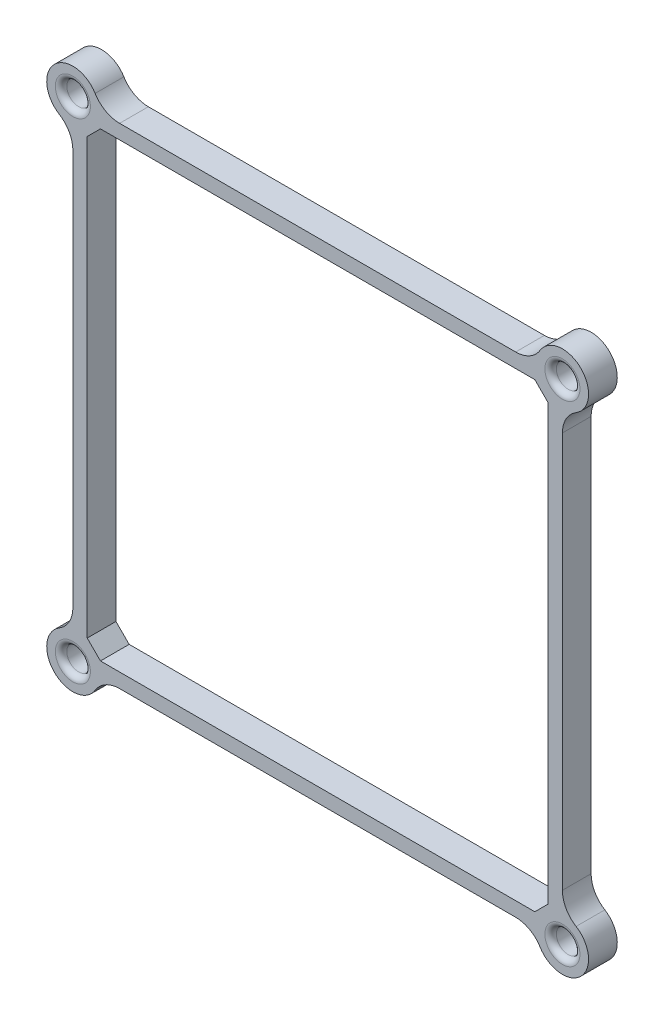
SolidWorks part; units mm, degrees
ref_plane "Front Plane" through (0, 0, 0) normal (0, 0, 1) x (1, 0, 0)
ref_plane "Top Plane" through (0, 0, 0) normal (0, 1, 0) x (1, 0, 0)
ref_plane "Right Plane" through (0, 0, 0) normal (1, 0, 0) x (0, 0, -1)
sketch "Sketch1" plane through (0, 0, 0) normal (0, 0, 1) x (1, 0, 0)
  line L0 (40.1, 0) -> (40.1, -80.2) construction
  line L1 (0, 0) -> (80.2, 0)
  line L2 (0, 0) -> (0, -80.2)
  line L3 (0, -80.2) -> (80.2, -80.2)
  line L4 (80.2, 0) -> (80.2, -80.2)
  line L6 (-2.5, 2.5) -> (82.7, 2.5)
  line L7 (-2.5, 2.5) -> (-2.5, -82.7)
  line L8 (-2.5, -82.7) -> (82.7, -82.7)
  line L9 (82.7, 2.5) -> (82.7, -82.7)
  line L10 (-2.5, 2.5) -> (82.7, -82.7) construction
  line L11 (-2.5, -82.7) -> (82.7, 2.5) construction
  circle A0 centre (-2.5, -82.7) radius 2.05
  circle A1 centre (-2.5, -82.7) radius 4.55
  circle A2 centre (82.7, -82.7) radius 2.05
  circle A3 centre (82.7, -82.7) radius 4.55
  circle A4 centre (82.7, 2.5) radius 2.05
  circle A5 centre (82.7, 2.5) radius 4.55
  circle A6 centre (-2.5, 2.5) radius 2.05
  circle A7 centre (-2.5, 2.5) radius 4.55
  point P7 (40.1, -40.1)
  dimension "D5" = 4.1
  dimension "D8" = 2.5
  dimension "D1" = 80.2
  dimension "D2" = 80.2
  dimension "D3" = 2.5
  dimension "D4" = 2.5
  dimension "D6" = 2
  dimension "D7" = 2
extrude "Boss-Extrude1" add sketch "Sketch1" along normal blind 5 contours A7 L7 A1 L2 | A7 L1 A5 L6 | A5 L4 A3 L9 | A3 L3 A1 L8 | L7 A7 L6 A6 | L6 A7 L7 A6 | L6 A5 L9 A4 | L9 A5 L6 A4 | L7 A1 L8 A0 | L8 A1 L7 A0 | L9 A3 L8 A2 | L8 A3 L9 A2
chamfer "Chamfer1" distance 2.3 angle 45 4 edges at (80.2, -80.2, 2.5) (0, -80.2, 2.5) (80.2, 0, 2.5) (0, 0, 2.5)
fillet "Fillet1" radius 5 8 edges at (-2.5, -78.15, 2.5) (2.05, -82.7, 2.5) (78.15, -82.7, 2.5) (82.7, -78.15, 2.5) (82.7, -2.05, 2.5) (78.15, 2.5, 2.5) (2.05, 2.5, 2.5) (-2.5, -2.05, 2.5)
fillet "Fillet2" radius 1 4 edges at (-0.45, -82.7, 5) (84.75, -82.7, 5) (84.75, 2.5, 5) (-0.45, 2.5, 5)
sketch "Sketch2" plane through (0, 0, 0) normal (0, 0, -1) x (-1, 0, 0)
  circle A0 centre (-82.7, 2.5) radius 4.55
  circle A1 centre (2.5, 2.5) radius 4.55
  circle A2 centre (2.5, -82.7) radius 4.55
  circle A3 centre (-82.7, -82.7) radius 4.55
extrude "Boss-Extrude2" add sketch "Sketch2" against normal blind 1
